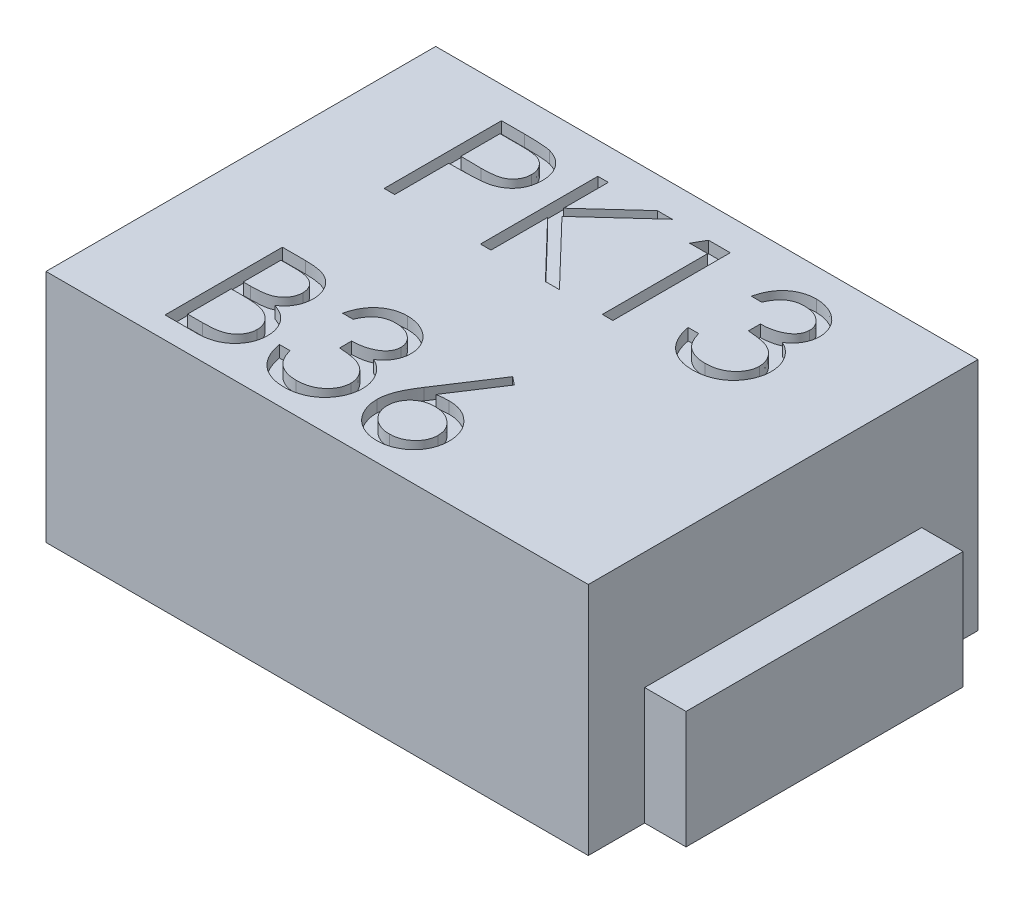
SolidWorks part; units mm, degrees
ref_plane "Plan de face" through (0, 0, 0) normal (0, 0, 1) x (1, 0, 0)
ref_plane "Plan de dessus" through (0, 0, 0) normal (0, 1, 0) x (1, 0, 0)
ref_plane "Plan de droite" through (0, 0, 0) normal (1, 0, 0) x (0, 0, -1)
sketch "Esquisse1" plane through (0, 0, 0) normal (0, 1, 0) x (1, 0, 0)
  line L0 (-2.6353, 0) -> (2.4471, 0) construction
  line L1 (-2.31, 1.66) -> (2.31, 1.66)
  line L2 (-2.31, 1.66) -> (-2.31, -1.66)
  line L3 (-2.31, -1.66) -> (2.31, -1.66)
  line L4 (2.31, 1.66) -> (2.31, -1.66)
  line L5 (0, 1.9882) -> (0, -1.7059) construction
  dimension "D1" = 4.62
  dimension "D2" = 3.32
extrude "Boss.-Extru.1" add sketch "Esquisse1" along normal blind 2
sketch "Esquisse2" plane through (0, 0, 0) normal (0, -1, 0) x (1, 0, 0)
  line L0 (0, 1.8166) -> (0, -1.8854) construction
  line L1 (-3.032, 0) -> (3.1609, 0) construction
  line L2 (-2.31, -1.66) -> (-2.31, 1.66) construction
  line L3 (-2.31, 1.18) -> (-2.6627, 1.18)
  line L4 (-2.31, 1.18) -> (-2.31, -1.18)
  line L5 (-2.31, -1.18) -> (-2.6627, -1.18)
  line L6 (-2.6627, 1.18) -> (-2.6627, -1.18)
  point P11 (-2.4863, -1.18)
  dimension "D1" = 2.36
  dimension "D2" = 0.3527
extrude "Boss.-Extru.2" add sketch "Esquisse2" against normal blind 1
mirror "Symétrie1" about plane through (0, 0, 0) normal (1, 0, 0) of "Boss.-Extru.2"
sketch "Esquisse3" plane through (0, 2, 0) normal (0, 1, 0) x (1, 0, 0)
  text T0 "PK13\r\nB36" font "Century Gothic" height 1
extrude "Enlèv. mat.-Extru.1" cut sketch "Esquisse3" against normal blind 0.1
